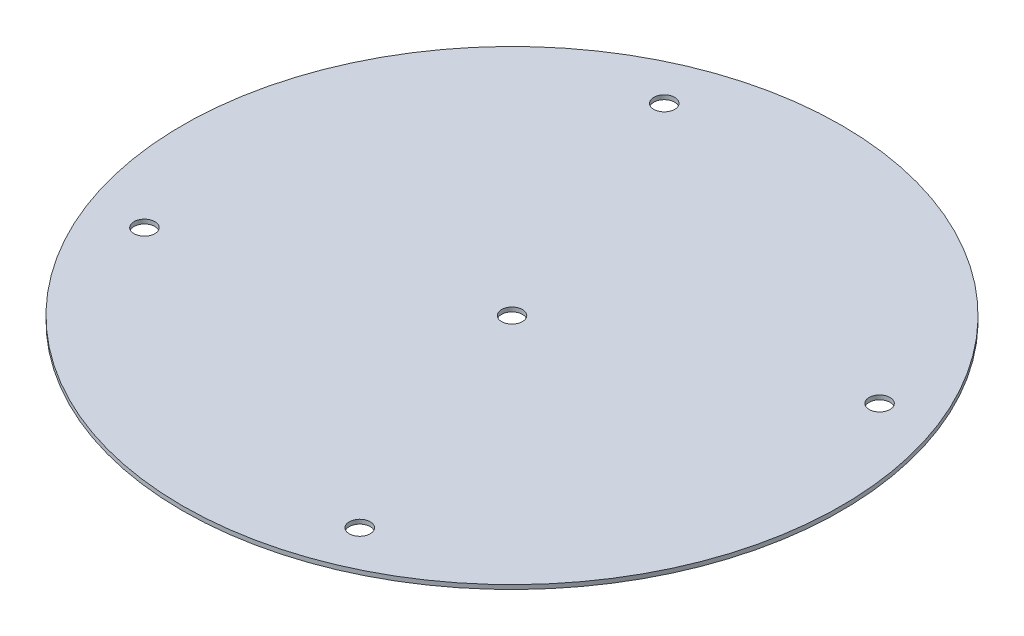
SolidWorks part; units mm, degrees
material "6061-T6 (SS)"
ref_plane "Front Plane" through (0, 0, 0) normal (0, 0, 1) x (1, 0, 0)
ref_plane "Top Plane" through (0, 0, 0) normal (0, 1, 0) x (1, 0, 0)
ref_plane "Right Plane" through (0, 0, 0) normal (1, 0, 0) x (0, 0, -1)
sketch "Sketch2" plane through (0, 0, 0) normal (1, 0, 0) x (0, 0, -1)
  line L0 (0, 0) -> (-77.55, 0)
  line L1 (-77.55, 0) -> (-77.55, 1)
  line L2 (-77.55, 1) -> (0, 1)
  line L5 (0, 1) -> (0, 0)
  dimension "D1" = 77.55
  dimension "D2" = 1
ref_axis "Axis1" through (0, -0.05, 0) along (0, 1, 0)
revolve "Revolve1" add sketch "Sketch2" angle 360 about axis through (0, -0.05, 0) along (0, 1, 0)
hole_wizard "#10 (0.1935) Diameter Hole1" positions "Sketch6" profile "Sketch7" hole size "#10" standard "ANSI Inch" end condition through all
sketch "Sketch6" plane through (0, 1, 0) normal (0, 1, 0) x (1, 0, 0)
  line L0 (0, 0) -> (-53.438, 129.0108) construction
  line L2 (0, 0) -> (0, 109.0908) construction
  point P0 (-25.3336, 61.1608)
  dimension "D1" = 22.5
  dimension "D2" = 66.2
sketch "Sketch7" plane through (-25.3336, 1, -61.1608) normal (1, 0, 0) x (0, 0, 1)
  line L0 (0, 0) -> (0, 1)
  line L1 (0, 1) -> (2.4574, 1)
  line L2 (2.4574, 1) -> (2.4574, 0)
  line L5 (2.4574, 0) -> (0, 0)
  line L11 (0, -6.35) -> (0, 107.95) construction
  dimension "Thru Hole Dia." = 4.9149
  dimension "Thru Hole Depth" = 1
pattern_circular "CirPattern3" count 4 over 360 about axis through (0, 0, 0) along (0, 1, 0) of "#10 (0.1935) Diameter Hole1"
hole_wizard "#10 (0.1935) Diameter Hole2" positions "Sketch8" profile "Sketch9" hole size "#10" standard "ANSI Inch" end condition through all
sketch "Sketch8" plane through (0, 1, 0) normal (0, 1, 0) x (1, 0, 0)
  line L0 (0, 0) -> (106.3094, -1.7118) construction
  point P7 (0, 0)
sketch "Sketch9" plane through (0, 1, 0) normal (1, 0, 0) x (0, 0, 1)
  line L0 (0, 0) -> (0, 1)
  line L1 (0, 1) -> (2.4574, 1)
  line L2 (2.4574, 1) -> (2.4574, 0)
  line L5 (2.4574, 0) -> (0, 0)
  line L11 (0, -6.35) -> (0, 107.95) construction
  dimension "Thru Hole Dia." = 4.9149
  dimension "Thru Hole Depth" = 1
equation "\"TubeDiameter\"= 6.500in"
equation "\"D1@Sketch2\"=\"TubeDiameter\"/2-5mm"
equation "\"D2@Sketch6\"=66.2"
